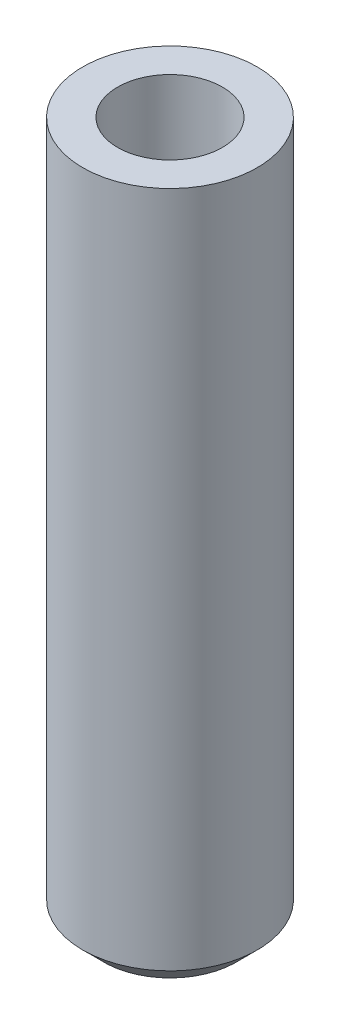
SolidWorks part; units mm, degrees
material "Glass"
ref_plane "Front Plane" through (0, 0, 0) normal (0, 0, 1) x (1, 0, 0)
ref_plane "Top Plane" through (0, 0, 0) normal (0, 1, 0) x (1, 0, 0)
ref_plane "Right Plane" through (0, 0, 0) normal (1, 0, 0) x (0, 0, -1)
sketch "Sketch1" plane through (0, 0, 0) normal (0, 0, 1) x (1, 0, 0)
  line L0 (0, 0) -> (3, 0) construction
  line L1 (3, 0) -> (5, 0)
  line L2 (3, 0) -> (3, 40)
  line L3 (3, 40) -> (5, 40)
  line L4 (5, 0) -> (5, 40)
  line L5 (0, 0) -> (0, 38.8189) construction
  dimension "D1" = 6
  dimension "D2" = 10
  dimension "D3" = 40
revolve "Revolve1" add sketch "Sketch1" angle 360 about L5
chamfer "Chamfer1" distance 1.2 angle 45 1 edges at (0, 0, -5)
